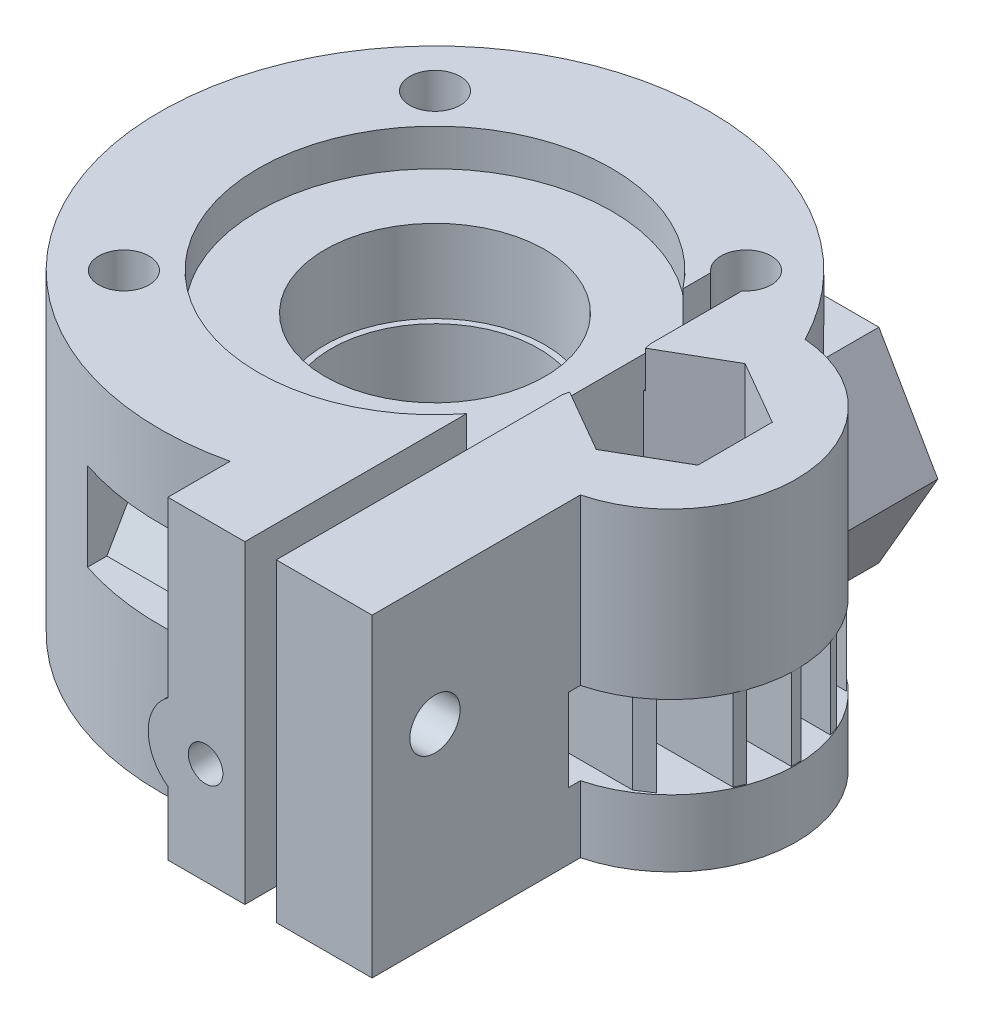
SolidWorks part; units mm, degrees
material "ABS"
ref_plane "Front Plane" through (0, 0, 0) normal (0, 0, 1) x (1, 0, 0)
ref_plane "Top Plane" through (0, 0, 0) normal (0, 1, 0) x (1, 0, 0)
ref_plane "Right Plane" through (0, 0, 0) normal (1, 0, 0) x (0, 0, -1)
ref_plane "Plane1" through (0, 4.25, 0) normal (0, 1, 0) x (1, 0, 0)
ref_plane "Plane2" through (0, 0, -18) normal (0, 0, 1) x (1, 0, 0)
ref_plane "Plane3" through (6.5, 0, 0) normal (-1, 0, 0) x (0, 0, 1)
sketch "Sketch1" plane through (0, 0, 0) normal (0, 1, 0) x (1, 0, 0)
  line L1 (4, -21) -> (17, -21)
  line L2 (4, -21) -> (4, -17.0367)
  line L4 (17, -21) -> (17, -7.746)
  arc A0 (15.575, 7.9793) -> (4, -17.0367) centre (0, 0) ccw
  arc A1 (17, -7.746) -> (15.575, 7.9793) centre (15, 0) ccw
  dimension "D1" = 35
  dimension "D2" = 16
  dimension "D3" = 15
  dimension "D4" = 4
  dimension "D5" = 21
  dimension "D7" = 13
extrude "Boss-Extrude1" add sketch "Sketch1" along normal blind 20
sketch "Sketch2" plane through (0, 20, 0) normal (0, 1, 0) x (1, 0, 0)
  line L0 (0, 0) -> (-9.8995, 9.8995) construction
  line L1 (9.8995, 9.8995) -> (0, 0) construction
  line L2 (-9.8995, -9.8995) -> (0, 0) construction
  line L3 (8.8995, -21) -> (8.8995, 8.6505)
  line L4 (4, -21) -> (17, -21) construction
  line L5 (8.8995, -21) -> (10.8995, -21)
  line L6 (10.8995, -21) -> (10.8995, 8.6505)
  line L7 (9.8995, 9.8995) -> (8.8995, 9.8995) construction
  line L8 (8.8995, 9.8995) -> (8.8995, 8.6505) construction
  line L9 (9.8995, 9.8995) -> (10.8995, 9.8995) construction
  line L10 (10.8995, 9.8995) -> (10.8995, 8.6505) construction
  circle A0 centre (0, 0) radius 6.6
  circle A1 centre (-9.8995, 9.8995) radius 1.6
  arc A2 (10.8995, 8.6505) -> (8.8995, 8.6505) centre (9.8995, 9.8995) ccw
  circle A3 centre (-9.8995, -9.8995) radius 1.6
  circle A4 centre (15, 0) radius 2.6
  dimension "D1" = 13.2
  dimension "D2" = 3.2
  dimension "D4" = 5.2
  dimension "D3" = 14
  dimension "D5" = 2
extrude "Cut-Extrude1" cut sketch "Sketch2" against normal up to next
sketch "Sketch3" plane through (0, 20, 0) normal (0, 1, 0) x (1, 0, 0)
  circle A0 centre (0, 0) radius 11.25
  dimension "D1" = 22.5
extrude "Cut-Extrude2" cut sketch "Sketch3" against normal blind 2.35
sketch "Sketch4" plane through (0, 17.65, 0) normal (0, 1, 0) x (1, 0, 0)
  circle A0 centre (0, 0) radius 7
  dimension "D1" = 14
extrude "Cut-Extrude3" cut sketch "Sketch4" against normal blind 5.25
sketch "Sketch5" plane through (0, 20, 0) normal (0, 1, 0) x (1, 0, 0)
  line L0 (10.8995, 2.7863) -> (10.8995, -2.7863) construction
  line L1 (19.1005, 2.3674) -> (15, 4.7349)
  line L2 (15, 4.7349) -> (10.8995, 2.3674)
  line L3 (10.8995, 2.3674) -> (10.8995, -2.3674)
  line L4 (10.8995, -2.3674) -> (15, -4.7349)
  line L5 (15, -4.7349) -> (19.1005, -2.3674)
  line L6 (19.1005, -2.3674) -> (19.1005, 2.3674)
  circle A0 centre (15, 0) radius 4.7349 construction
extrude "Cut-Extrude4" cut sketch "Sketch5" against normal blind 6
sketch "Sketch6" plane through (0, 4.25, 0) normal (0, 1, 0) x (1, 0, 0)
  line L0 (15, 8.5) -> (23.5, 8.5)
  line L1 (23.5, 8.5) -> (23.5, 0)
  line L2 (23.5, 0) -> (23.5, -8.5)
  line L3 (23.5, -8.5) -> (15, -8.5)
  line L4 (15, 0) -> (2.8261, 0) construction
  line L5 (5, 0) -> (5, 4)
  line L6 (5, 4) -> (7.5, 4)
  line L7 (5, 0) -> (5, -4)
  line L8 (5, -4) -> (7.5, -4)
  arc A0 (7.5, -4) -> (15, -8.5) centre (15, 0) ccw
  arc A1 (15, 8.5) -> (7.5, 4) centre (15, 0) ccw
  dimension "D1" = 17
  dimension "D2" = 8
  dimension "D3" = 10
extrude "Cut-Extrude5" cut sketch "Sketch6" along normal blind 5.25
sketch "Sketch10" plane through (0, 0, 21) normal (0, 0, 1) x (1, 0, 0)
  line L0 (4, 0) -> (8.8995, 0) construction
  circle A0 centre (5.75, 6.5) radius 3
  dimension "D1" = 6
  dimension "D2" = 6.5
  dimension "D3" = 5.75
extrude "Boss-Extrude2" add sketch "Sketch10" against normal up to next
sketch "Sketch11" plane through (0, 0, -18) normal (0, 0, 1) x (1, 0, 0)
  line L0 (-17.5, 0) -> (15.575, 0) construction
  line L1 (-1.0056, 6.5) -> (2.7472, 0)
  line L2 (2.7472, 0) -> (10.2528, 0)
  line L3 (10.2528, 0) -> (14.0056, 6.5)
  line L4 (14.0056, 6.5) -> (10.2528, 13)
  line L5 (10.2528, 13) -> (2.7472, 13)
  line L6 (2.7472, 13) -> (-1.0056, 6.5)
  circle A0 centre (6.5, 6.5) radius 7.5056 construction
  dimension "D1" = 6.5
  dimension "D2" = 6.5
extrude "Boss-Extrude3" add sketch "Sketch11" along normal up to next
sketch "Sketch8" plane through (0, 0, 21) normal (0, 0, 1) x (1, 0, 0)
  line L0 (8.8995, 0) -> (8.8995, 20) construction
  line L1 (4, 0) -> (8.8995, 0) construction
  circle A0 centre (6.3995, 6.5) radius 1.1
  dimension "D1" = 2.2
  dimension "D2" = 2.5
  dimension "D3" = 6.5
extrude "Cut-Extrude6" cut sketch "Sketch8" against normal through all
sketch "Sketch13" plane through (6.5, 0, 0) normal (-1, 0, 0) x (0, 0, 1)
  line L0 (-18, 6.5) -> (-4, 6.5) construction
  line L1 (-18, 7.6) -> (-18, 5.4) construction
  line L2 (-6, 6.5) -> (-4, 6.5)
  line L3 (-4, 8.6782) -> (-4, 6.5)
  line L4 (-4, 8.6782) -> (-6, 7)
  line L5 (-6, 7) -> (-6, 6.5)
  line L7 (-4, 5.4) -> (-4, 7.6) construction
  dimension "D2" = 0.5
  dimension "D4" = 6
  dimension "D5" = 40
revolve "Cut-Revolve1" cut sketch "Sketch13" angle 360 about L0
sketch "Sketch14" plane through (0, 0, -18) normal (0, 0, -1) x (-1, 0, 0)
  circle A0 centre (-6.3995, 6.5) radius 2.25
  dimension "D1" = 4.5
extrude "Cut-Extrude7" cut sketch "Sketch14" against normal blind 5
sketch "Sketch15" plane through (17, 0, 0) normal (1, 0, 0) x (0, 0, -1)
  line L0 (-21, 0) -> (-7.746, 0) construction
  circle A0 centre (-17, 12) radius 1.6
  dimension "D1" = 3.2
  dimension "D2" = 12
  dimension "D3" = 17
extrude "Cut-Extrude8" cut sketch "Sketch15" against normal up to surface (13 mm away) up to face at (4, 14.4683, 19.0184)
sketch "Sketch16" plane through (4, 0, 0) normal (-1, 0, 0) x (0, 0, 1)
  line L1 (20.2332, 12) -> (18.6166, 14.8)
  line L2 (18.6166, 14.8) -> (15.3834, 14.8)
  line L3 (15.3834, 14.8) -> (13.7668, 12)
  line L4 (13.7668, 12) -> (15.3834, 9.2)
  line L5 (15.3834, 9.2) -> (18.6166, 9.2)
  line L6 (18.6166, 9.2) -> (20.2332, 12)
  circle A0 centre (17, 12) radius 2.8 construction
  dimension "D1" = 5.6
extrude "Cut-Extrude9" cut sketch "Sketch16" against normal blind 1.5 and the other way blind 9.5
sketch "Sketch17" plane through (0, 4.25, 0) normal (0, 1, 0) x (1, 0, 0)
  line L0 (12.3809, 0.35) -> (12.3809, -0.25)
  line L1 (5.2498, 4) -> (5.2498, 3.3308) construction
  line L2 (5.2498, -4) -> (7.5, -4) construction
  line L3 (22.2377, 3.3308) -> (10.8995, 3.3308)
  line L4 (22.478, -2.647) -> (10.8995, -2.647)
  line L5 (20.1005, -6) -> (10.8995, -6)
  line L6 (22.9339, -0.25) -> (17.6468, -0.25)
  line L7 (10.8995, -6) -> (10.8995, -6.6)
  line L8 (10.8995, -2.3674) -> (10.8995, -2.7863) construction
  line L10 (22.9339, 0.35) -> (17.6468, 0.35)
  line L11 (10.8995, 6.25) -> (10.8995, 5.65)
  line L12 (22.4401, 2.7308) -> (10.8995, 2.7308)
  line L13 (5.2498, -0.25) -> (5.2498, -2.647) construction
  line L16 (10.8995, 6.25) -> (19.8956, 6.25)
  line L17 (17.6468, 0.35) -> (17.6468, -0.25)
  line L18 (20.5305, 5.65) -> (10.8995, 5.65)
  line L19 (12.3809, 0.35) -> (10.8995, 0.35)
  line L22 (10.8995, -2.647) -> (10.8995, -3.247)
  line L23 (12.3809, -0.25) -> (10.8995, -0.25)
  line L24 (22.2171, -3.247) -> (10.8995, -3.247)
  line L25 (8.8995, -3.247) -> (8.8995, -2.647)
  line L28 (8.8995, 3.3308) -> (7.1798, 3.3308)
  line L29 (8.8995, 2.7308) -> (6.9506, 2.7308)
  line L30 (19.1871, -6.6) -> (10.8995, -6.6)
  line L31 (10.8995, 0.35) -> (10.8995, -0.25)
  line L34 (5.2498, 2.7308) -> (5.2498, 0.25) construction
  line L35 (5.2498, -3.247) -> (5.2498, -4) construction
  line L36 (10.8995, 3.3308) -> (10.8995, 2.7308)
  line L37 (8.8995, 0.35) -> (6.6227, 0.35)
  line L38 (8.8995, -0.25) -> (6.6227, -0.25)
  line L39 (8.8995, -2.647) -> (6.9227, -2.647)
  line L40 (8.8995, -3.247) -> (7.1446, -3.247)
  line L41 (8.8995, -0.25) -> (8.8995, 0.35)
  line L42 (8.8995, 2.7308) -> (8.8995, 3.3308)
  line L43 (7.1798, 3.3308) -> (5.7593, 3.3308)
  line L44 (6.9506, 2.7308) -> (6.0784, 2.7308)
  line L45 (6.0784, 2.7308) -> (5.7593, 3.3308)
  line L46 (6.6227, 0.35) -> (6.6227, -0.25)
  line L47 (6.9227, -2.647) -> (6.046, -2.647)
  line L48 (7.1446, -3.247) -> (5.8006, -3.247)
  line L49 (5.8006, -3.247) -> (6.046, -2.647)
  line L50 (20.1005, -6) -> (19.1871, -6.6)
  line L51 (22.478, -2.647) -> (22.2171, -3.247)
  line L52 (22.9339, 0.35) -> (22.9339, -0.25)
  line L53 (22.2377, 3.3308) -> (22.4401, 2.7308)
  line L54 (19.8956, 6.25) -> (20.5305, 5.65)
  circle A0 centre (15, 0) radius 8.5 construction
  circle A1 centre (0, 0) radius 6.6 construction
  arc A2 (5.2498, -4) -> (5.2498, 4) centre (0, 0) ccw construction
  circle A3 centre (0, 0) radius 6.6 construction
  point P16 (15, 3)
  point P21 (15, 6)
  point P26 (15, -3)
  point P31 (15, -6)
  dimension "D1" = 17
  dimension "D8" = 0.6
  dimension "D2" = 8
  dimension "D3" = 0.6
  dimension "D4" = 3
  dimension "D5" = 3
  dimension "D6" = 3
  dimension "D7" = 3
  dimension "D9" = 0.6
  dimension "D10" = 0.6
extrude "Boss-Extrude4" add sketch "Sketch17" along normal up to next
equation "\"D8@Sketch17\"=\"D3@Sketch17\""
equation "\"D9@Sketch17\"=\"D3@Sketch17\""
equation "\"D10@Sketch17\"=\"D3@Sketch17\""
